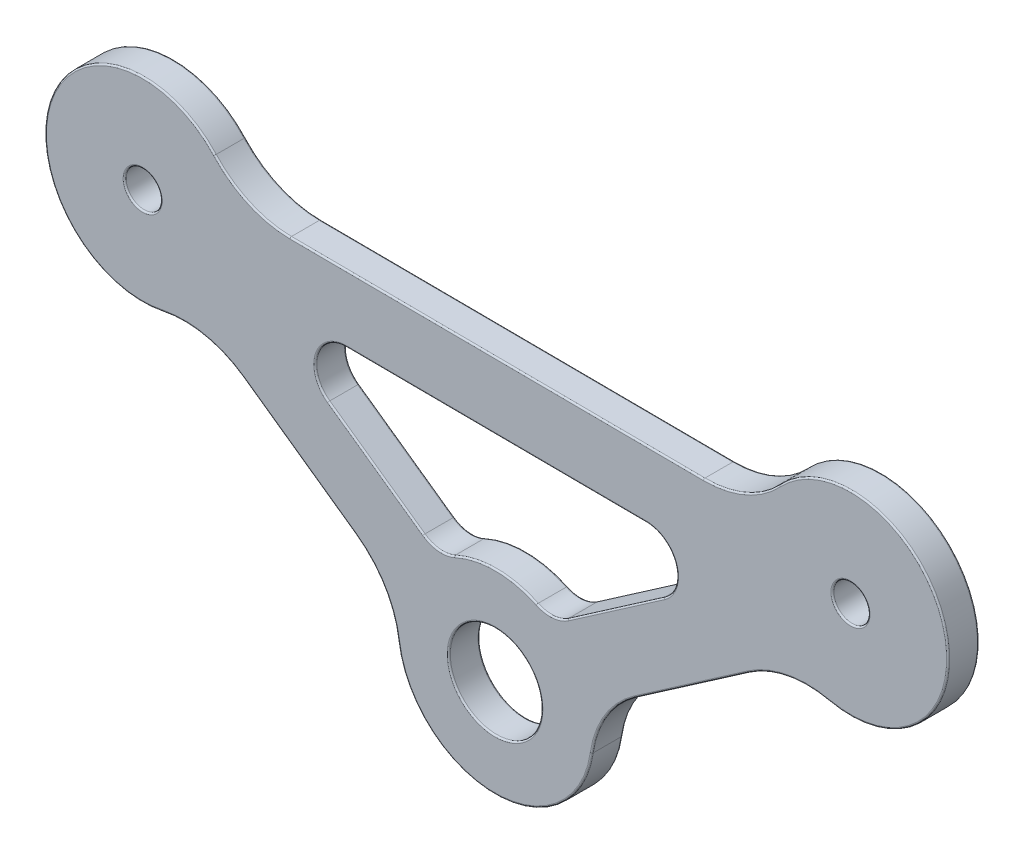
SolidWorks part; units mm, degrees
ref_plane "Płaszczyzna przednia" through (0, 0, 0) normal (0, 0, 1) x (1, 0, 0)
ref_plane "Płaszczyzna górna" through (0, 0, 0) normal (0, 1, 0) x (1, 0, 0)
ref_plane "Płaszczyzna prawa" through (0, 0, 0) normal (1, 0, 0) x (0, 0, -1)
sketch "Szkic1" plane through (0, 0, 0) normal (0, 0, 1) x (1, 0, 0)
  line L0 (-52.6671, 201.9794) -> (-18.1175, 225.861) construction
  line L1 (-86.9251, 226.2774) -> (-52.6671, 201.9794) construction
  line L2 (-18.1175, 225.861) -> (-86.9251, 226.2774) construction
  line L3 (-52.6671, 201.9794) -> (-18.1175, 225.861) construction
  line L4 (-86.9251, 226.2774) -> (-52.6671, 201.9794) construction
  line L5 (-18.1175, 225.861) -> (-86.9251, 226.2774) construction
sketch "Szkic2" plane through (0, 0, 0) normal (0, 0, 1) x (1, 0, 0)
  circle A0 centre (-86.9251, 226.2774) radius 9.5
  circle A1 centre (-52.6671, 201.9794) radius 9.5
  circle A2 centre (-18.1175, 225.861) radius 9.5
  circle A3 centre (-52.6671, 201.9794) radius 4.5
  circle A4 centre (-86.9251, 226.2774) radius 1.75
  circle A5 centre (-18.1175, 225.861) radius 1.75
  dimension "D1" = 19
  dimension "D2" = 9
  dimension "D3" = 3.5
extrude "Dodanie-wyciągnięcie1" add sketch "Szkic2" against normal blind 3
sketch "Szkic3" plane through (0, 0, 0) normal (0, 0, 1) x (1, 0, 0)
  line L0 (-47.7314, 205.3911) -> (-23.0532, 222.4493)
  line L1 (-52.6671, 201.9794) -> (-18.1175, 225.861) construction
  line L2 (-25.0213, 225.9028) -> (-80.0213, 226.2356)
  line L3 (-18.1175, 225.861) -> (-86.9251, 226.2774) construction
  line L4 (-82.0311, 222.8062) -> (-57.5611, 205.4505)
  line L5 (-86.9251, 226.2774) -> (-52.6671, 201.9794) construction
  point P12 (-69.7961, 214.1284)
  point P13 (-52.5213, 226.0692)
  point P14 (-35.3923, 213.9202)
  dimension "D1" = 55
  dimension "D2" = 30
extrude "Wyciągnięcie-cienka ścianka1" add sketch "Szkic3" against normal blind 3 thin thin type mid plane wall 6.5
fillet "Zaokrąglenie1" radius 3 2 edges at (-47.1718, 209.7287, -1.5) (-58.0681, 209.7947, -1.5)
fillet "Zaokrąglenie2" radius 3 1 edges at (-28.4447, 222.6734, -1.5)
fillet "Zaokrąglenie3" radius 3 1 edges at (-76.6372, 222.965, -1.5)
fillet "Zaokrąglenie6" radius 10 6 edges at (-77.9788, 229.4733, -1.5) (-27.0245, 229.1649, -1.5) (-23.6128, 218.1117, -1.5) (-43.4758, 204.3818, -1.5) (-61.8285, 204.4928, -1.5) (-81.524, 218.4621, -1.5)
fillet "Zaokrąglenie7" radius 0.15 46 edges at (-48.1671, 201.9794, -3) (-16.3675, 225.861, -3) (-85.1751, 226.2774, -3) (-63.4354, 204.6073, -3) (-52.7246, 192.4796, -3) (-41.8677, 204.4768, -3) (-33.5443, 211.2467, -3) (-33.5443, 211.2467, 0) (-24.27, 216.6408, -3) (-9.0401, 228.6628, -3) (-28.3963, 230.0095, -3) (-52.5016, 229.3191, -3) (-52.5016, 229.3191, 0) (-76.5968, 230.3012, -3) (-95.9679, 229.1888, -3) (-80.8847, 216.9834, -3) (-71.6763, 211.4775, -3) (-71.6763, 211.4775, 0) (-47.0725, 210.286, -3) (-52.6096, 211.4792, -3) (-58.1607, 210.3531, -3) (-64.2465, 214.1768, -3) (-64.2465, 214.1768, 0) (-69.9964, 220.8269, -3) (-52.541, 222.8192, 0) (-52.541, 222.8192, -3) (-35.1109, 220.6158, -3) (-40.9408, 214.0357, 0) (-40.9408, 214.0357, -3) (-48.1671, 201.9794, 0) (-16.3675, 225.861, 0) (-85.1751, 226.2774, 0) (-28.3963, 230.0095, 0) (-9.0401, 228.6628, 0) (-24.27, 216.6408, 0) (-41.8677, 204.4768, 0) (-52.7246, 192.4796, 0) (-63.4354, 204.6073, 0) (-80.8847, 216.9834, 0) (-95.9679, 229.1888, 0) (-76.5968, 230.3012, 0) (-58.1607, 210.3531, 0) (-52.6096, 211.4792, 0) (-47.0725, 210.286, 0) (-35.1109, 220.6158, 0) (-69.9964, 220.8269, 0)
